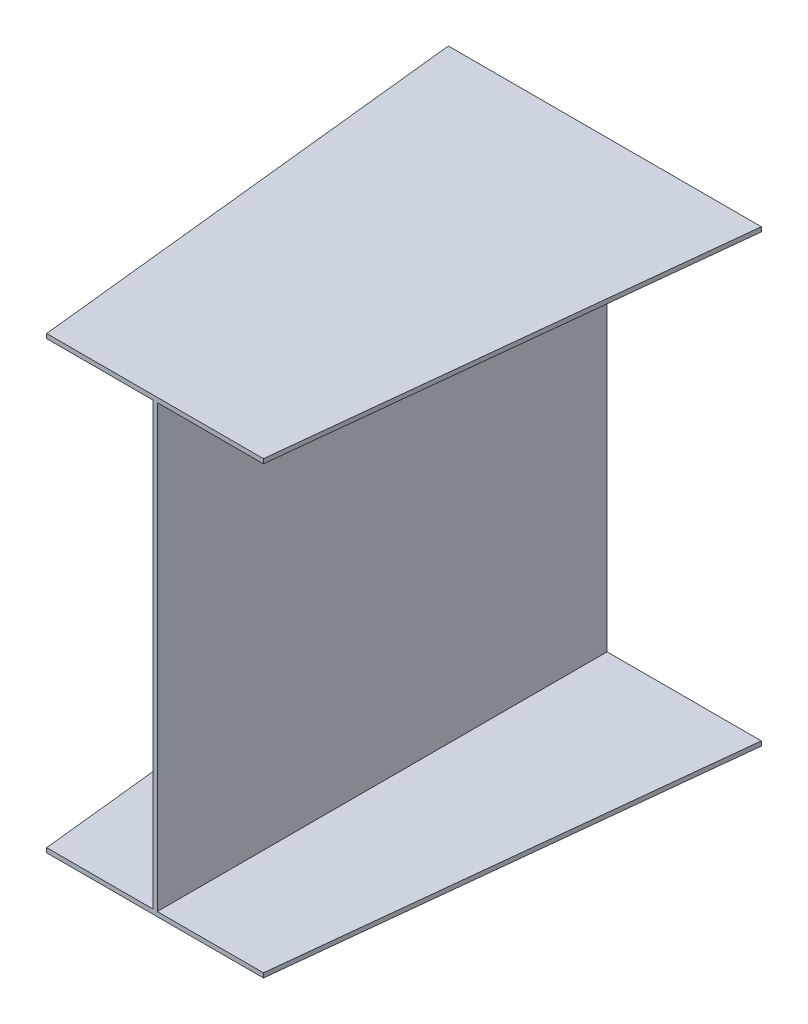
SolidWorks part; units mm, degrees
ref_plane "Front Plane" through (0, 0, 0) normal (0, 0, 1) x (1, 0, 0)
ref_plane "Top Plane" through (0, 0, 0) normal (0, 1, 0) x (1, 0, 0)
ref_plane "Right Plane" through (0, 0, 0) normal (1, 0, 0) x (0, 0, -1)
sketch "Sketch1" plane through (0, 0, 0) normal (0, 0, 1) x (1, 0, 0)
  line L0 (10, 980) -> (353, 980)
  line L2 (0, 0) -> (0, 980)
  line L4 (10, 0) -> (10, 980)
  line L5 (-343, 980) -> (0, 980)
  line L6 (-343, 980) -> (-343, 990)
  line L7 (-343, 990) -> (353, 990)
  line L8 (353, 980) -> (353, 990)
  line L9 (-343, 0) -> (0, 0)
  line L10 (-343, 0) -> (-343, -10)
  line L11 (-343, -10) -> (353, -10)
  line L12 (353, 0) -> (353, -10)
  line L13 (10, 0) -> (353, 0)
  dimension "D1" = 10
  dimension "D2" = 980
  dimension "D3" = 10
  dimension "D4" = 696
  dimension "D5" = 343
  dimension "D6" = 10
  dimension "D7" = 343
ref_plane "Plane1" through (0, 0, 1000) normal (0, 0, 1) x (1, 0, 0)
ref_plane "Plane2" through (0, 0, 1000) normal (0, 0, 1) x (1, 0, 0)
sketch "Sketch4" plane through (0, 0, 1000) normal (0, 0, 1) x (1, 0, 0)
  line L0 (10, 0) -> (10, 980) construction
  line L2 (0, 0) -> (0, 980)
  line L4 (10, 0) -> (10, 980)
  line L5 (-343, 0) -> (0, 0) construction
  line L6 (-236, 0) -> (0, 0)
  line L7 (-236, 0) -> (-236, -10)
  line L8 (-236, -10) -> (246, -10)
  line L9 (246, 0) -> (246, -10)
  line L10 (-343, -10) -> (353, -10) construction
  line L11 (-236, 980) -> (0, 980)
  line L12 (-236, 990) -> (-236, 980)
  line L13 (-236, 990) -> (246, 990)
  line L14 (246, 990) -> (246, 980)
  line L15 (10, 980) -> (246, 980)
  line L16 (10, 0) -> (246, 0)
  dimension "D1" = 482
  dimension "D2" = 236
  dimension "D3" = 980
  dimension "D4" = 236
loft "Loft3" add profiles "Sketch1", "Sketch4"
